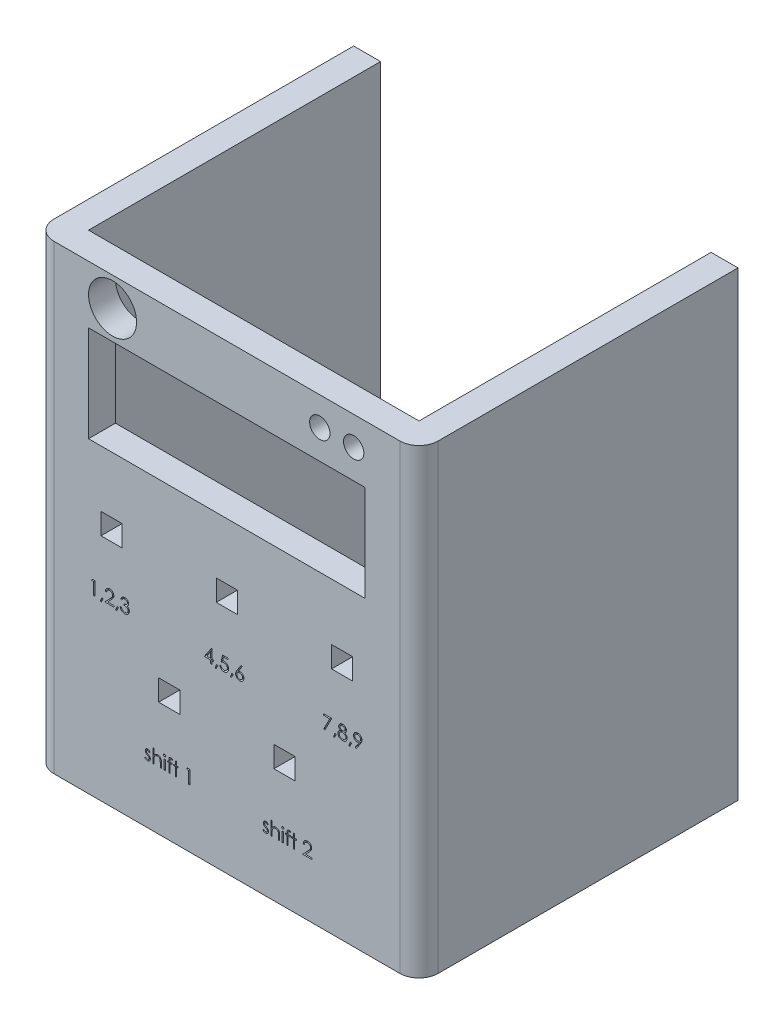
SolidWorks part; units mm, degrees
ref_plane "정면" through (0, 0, 0) normal (0, 0, 1) x (1, 0, 0)
ref_plane "윗면" through (0, 0, 0) normal (0, 1, 0) x (1, 0, 0)
ref_plane "우측면" through (0, 0, 0) normal (1, 0, 0) x (0, 0, -1)
sketch "스케치7" plane through (0, 0, 0) normal (0, 1, 0) x (1, 0, 0)
  line L0 (-50, 45) -> (50, 45) construction
  line L1 (-50, -45) -> (50, -45)
  line L2 (-50, -45) -> (-50, 45)
  line L3 (-50, 45) -> (50, 45)
  line L4 (50, -45) -> (50, 45)
  line L5 (-50, -45) -> (50, 45) construction
  line L6 (-50, 45) -> (50, -45) construction
  point P0 (0, 0)
  dimension "D1" = 90
  dimension "D2" = 100
extrude "보스-돌출5" add sketch "스케치7" along normal blind 120
sketch "스케치9" plane through (0, 120, 0) normal (0, 1, 0) x (1, 0, 0)
  line L0 (50, 45) -> (-50, 45) construction
  line L1 (-43, -38) -> (43, -38)
  line L2 (-43, -38) -> (-43, 38)
  line L3 (-43, 38) -> (43, 38)
  line L4 (43, -38) -> (43, 38)
  line L5 (-43, -38) -> (43, 38) construction
  line L6 (-43, 38) -> (43, -38) construction
  line L7 (-50, 45) -> (-50, -45) construction
  point P0 (0, 0)
  dimension "D1" = 7
  dimension "D2" = 7
extrude "컷-돌출4" cut sketch "스케치9" against normal blind 115
fillet "필렛2" radius 5 2 edges at (50, 60, 45) (-50, 60, 45)
sketch "스케치10" plane through (0, 0, 45) normal (0, 0, 1) x (1, 0, 0)
  line L0 (-45, 120) -> (45, 120) construction
  line L5 (0, -49.5) -> (0, 49.5) construction
  line L6 (-36, 105) -> (36, 105)
  line L7 (-36, 105) -> (-36, 80)
  line L8 (-36, 80) -> (36, 80)
  line L9 (36, 105) -> (36, 80)
  line L10 (-36, 105) -> (36, 80) construction
  line L11 (-36, 80) -> (36, 105) construction
  point P0 (0, 92.5)
  dimension "D1" = 72
  dimension "D2" = 25
  dimension "D3" = 15
extrude "컷-돌출6" cut sketch "스케치10" against normal blind 11
sketch "스케치11" plane through (0, 120, 0) normal (0, 1, 0) x (1, 0, 0)
  line L0 (43, 38) -> (50, 38) construction
  line L1 (50, -40) -> (50, 45) construction
  line L3 (50, 38) -> (-50, 38)
  line L4 (50, 38) -> (50, 45)
  line L5 (50, 45) -> (-50, 45)
  line L6 (-50, 38) -> (-50, 45)
extrude "컷-돌출7" cut sketch "스케치11" against normal blind 120
sketch "스케치12" plane through (0, 0, 45) normal (0, 0, 1) x (1, 0, 0)
  line L0 (45, 0) -> (45, 120) construction
  circle A0 centre (33, 112.5776) radius 2.65
  dimension "D1" = 5.3
  dimension "D2" = 12
extrude "컷-돌출8" cut sketch "스케치12" against normal blind 120
sketch "스케치13" plane through (0, 0, 45) normal (0, 0, 1) x (1, 0, 0)
  line L0 (24.1835, 115.2114) -> (33, 115.2276) construction
  circle A0 centre (24.1835, 112.5614) radius 2.65
  circle A1 centre (33, 112.5776) radius 2.65 construction
  dimension "D1" = 5.3
extrude "컷-돌출9" cut sketch "스케치13" against normal blind 120
sketch "스케치17" plane through (0, 0, 38) normal (0, 0, -1) x (-1, 0, 0)
  line L0 (-36, 105) -> (-36, 80) construction
  line L1 (-36, 92.5) -> (-36, 86.5)
  line L2 (-36, 86.5) -> (-40.5, 86.5)
  line L3 (-36, 92.5) -> (-36, 98.5)
  line L4 (-36, 98.5) -> (-40.5, 98.5)
  line L5 (-40.5, 98.5) -> (-40.5, 86.5)
extrude "컷-돌출10" cut sketch "스케치17" against normal blind 3.5
sketch "스케치20" plane through (0, 0, 45) normal (0, 0, 1) x (1, 0, 0)
  line L0 (-30, 80) -> (-30, 62.5) construction
  line L1 (-36, 80) -> (36, 80) construction
  line L2 (-30, 71.25) -> (-50, 71.25) construction
  line L4 (-2.75, 59.75) -> (2.75, 59.75)
  line L5 (-50, 0) -> (-50, 120) construction
  line L6 (-30, 71.25) -> (0, 71.25) construction
  line L7 (0, 80.6671) -> (0, 62.5) construction
  line L8 (0, -45.65) -> (0, 45.65) construction
  line L9 (0, 71.25) -> (30, 71.25) construction
  line L10 (30, 80) -> (30, 62.5) construction
  line L11 (30, 71.25) -> (50, 71.25) construction
  line L12 (50, 120) -> (50, 0) construction
  line L13 (-2.75, 59.75) -> (-2.75, 65.25)
  line L14 (-32.75, 59.75) -> (-27.25, 59.75)
  line L15 (-32.75, 59.75) -> (-32.75, 65.25)
  line L16 (-32.75, 65.25) -> (-27.25, 65.25)
  line L17 (-27.25, 59.75) -> (-27.25, 65.25)
  line L18 (-32.75, 59.75) -> (-27.25, 65.25) construction
  line L19 (-32.75, 65.25) -> (-27.25, 59.75) construction
  line L20 (-2.75, 65.25) -> (2.75, 65.25)
  line L21 (2.75, 59.75) -> (2.75, 65.25)
  line L22 (-2.75, 59.75) -> (2.75, 65.25) construction
  line L23 (-2.75, 65.25) -> (2.75, 59.75) construction
  line L24 (27.25, 65.25) -> (32.75, 65.25)
  line L25 (27.25, 65.25) -> (27.25, 59.75)
  line L26 (27.25, 59.75) -> (32.75, 59.75)
  line L27 (32.75, 65.25) -> (32.75, 59.75)
  line L28 (27.25, 65.25) -> (32.75, 59.75) construction
  line L29 (27.25, 59.75) -> (32.75, 65.25) construction
  dimension "D1" = 5.5
  dimension "D2" = 5.5
  dimension "D3" = 20
  dimension "D4" = 5.5
  dimension "D5" = 5.5
  dimension "D6" = 30
  dimension "D7" = 5.5
  dimension "D8" = 5.5
  dimension "D9" = 17.5
  dimension "D10" = 17.5
  dimension "D11" = 17.5
  dimension "D12" = 30
  dimension "D13" = 20
extrude "컷-돌출11" cut sketch "스케치20" against normal blind 19.6
sketch "스케치22" plane through (0, 0, 45) normal (0, 0, 1) x (1, 0, 0)
  line L0 (-27.25, 62.5) -> (-2.75, 62.5) construction
  line L1 (-27.25, 59.75) -> (-27.25, 65.25) construction
  line L2 (-2.75, 65.25) -> (-2.75, 59.75) construction
  line L3 (-15, 62.5) -> (-15, 32.5) construction
  line L4 (2.75, 62.5) -> (27.25, 62.5) construction
  line L5 (-17.75, 29.75) -> (-12.25, 29.75)
  line L6 (-17.75, 29.75) -> (-17.75, 35.25)
  line L7 (-17.75, 35.25) -> (-12.25, 35.25)
  line L8 (-12.25, 29.75) -> (-12.25, 35.25)
  line L9 (-17.75, 29.75) -> (-12.25, 35.25) construction
  line L10 (-17.75, 35.25) -> (-12.25, 29.75) construction
  line L11 (2.75, 59.75) -> (2.75, 65.25) construction
  line L12 (27.25, 65.25) -> (27.25, 59.75) construction
  line L13 (27.25, 62.5) -> (15, 62.5) construction
  line L14 (15, 62.5) -> (15, 32.5) construction
  line L16 (12.25, 29.75) -> (17.75, 29.75)
  line L17 (12.25, 29.75) -> (12.25, 35.25)
  line L18 (12.25, 35.25) -> (17.75, 35.25)
  line L19 (17.75, 29.75) -> (17.75, 35.25)
  line L20 (12.25, 29.75) -> (17.75, 35.25) construction
  line L21 (12.25, 35.25) -> (17.75, 29.75) construction
  dimension "D1" = 5.5
  dimension "D2" = 5.5
  dimension "D3" = 5.5
  dimension "D4" = 5.5
  dimension "D5" = 30
  dimension "D6" = 30
  dimension "D7" = 30
extrude "컷-돌출12" cut sketch "스케치22" against normal blind 19.6
sketch "스케치28" plane through (0, 0, 45) normal (0, 0, 1) x (1, 0, 0)
  line L0 (-36, 105) -> (-29.75, 105) construction
  line L1 (36, 105) -> (-36, 105) construction
  line L2 (-29.75, 105) -> (-29.75, 120) construction
  line L3 (-45, 120) -> (45, 120) construction
  circle A0 centre (-29.75, 112.5) radius 6.25
extrude "컷-돌출14" cut sketch "스케치28" against normal blind 7
sketch "스케치29" plane through (-50, 0, 0) normal (-1, 0, 0) x (0, 0, 1)
  line L0 (45, 21) -> (20, 21) construction
  line L1 (45, 120) -> (45, 0) construction
  line L2 (35, 14) -> (45, 14) construction
  line L3 (20, 21) -> (20, 0) construction
  line L4 (45.65, 0) -> (-45.65, 0) construction
  line L5 (27.5, 7) -> (27.5, 0) construction
  line L6 (20, 21) -> (35, 21)
  line L7 (20, 21) -> (20, 7)
  line L8 (20, 7) -> (35, 7)
  line L9 (35, 21) -> (35, 7)
  line L10 (-38, 0) -> (40, 0) construction
  dimension "D1" = 15
  dimension "D2" = 14
extrude "컷-돌출15" cut sketch "스케치29" against normal blind 10
sketch "스케치32" plane through (-50, 0, 0) normal (-1, 0, 0) x (0, 0, 1)
  line L0 (27.9563, 0) -> (27.9563, 5) construction
  line L1 (-38, 0) -> (40, 0) construction
  line L2 (27.9563, 5) -> (27.9563, 7) construction
  line L3 (20, 7) -> (35, 7) construction
sketch "스케치33" plane through (0, 0, 45) normal (0, 0, 1) x (1, 0, 0)
  text T0 "1,2,3"
extrude "컷-돌출16" cut sketch "스케치33" against normal blind 2
sketch "스케치34" plane through (0, 0, 45) normal (0, 0, 1) x (1, 0, 0)
  text T0 "4,5,6"
  point P1 (0, 0)
extrude "컷-돌출17" cut sketch "스케치34" against normal blind 2
sketch "스케치35" plane through (0, 0, 45) normal (0, 0, 1) x (1, 0, 0)
  text T0 "7,8,9"
extrude "컷-돌출18" cut sketch "스케치35" against normal blind 2
sketch "스케치36" plane through (0, 0, 45) normal (0, 0, 1) x (1, 0, 0)
  text T0 "shift 1"
extrude "컷-돌출19" cut sketch "스케치36" against normal blind 2
sketch "스케치37" plane through (0, 0, 45) normal (0, 0, 1) x (1, 0, 0)
  text T0 "shift 2"
extrude "컷-돌출20" cut sketch "스케치37" against normal blind 2
